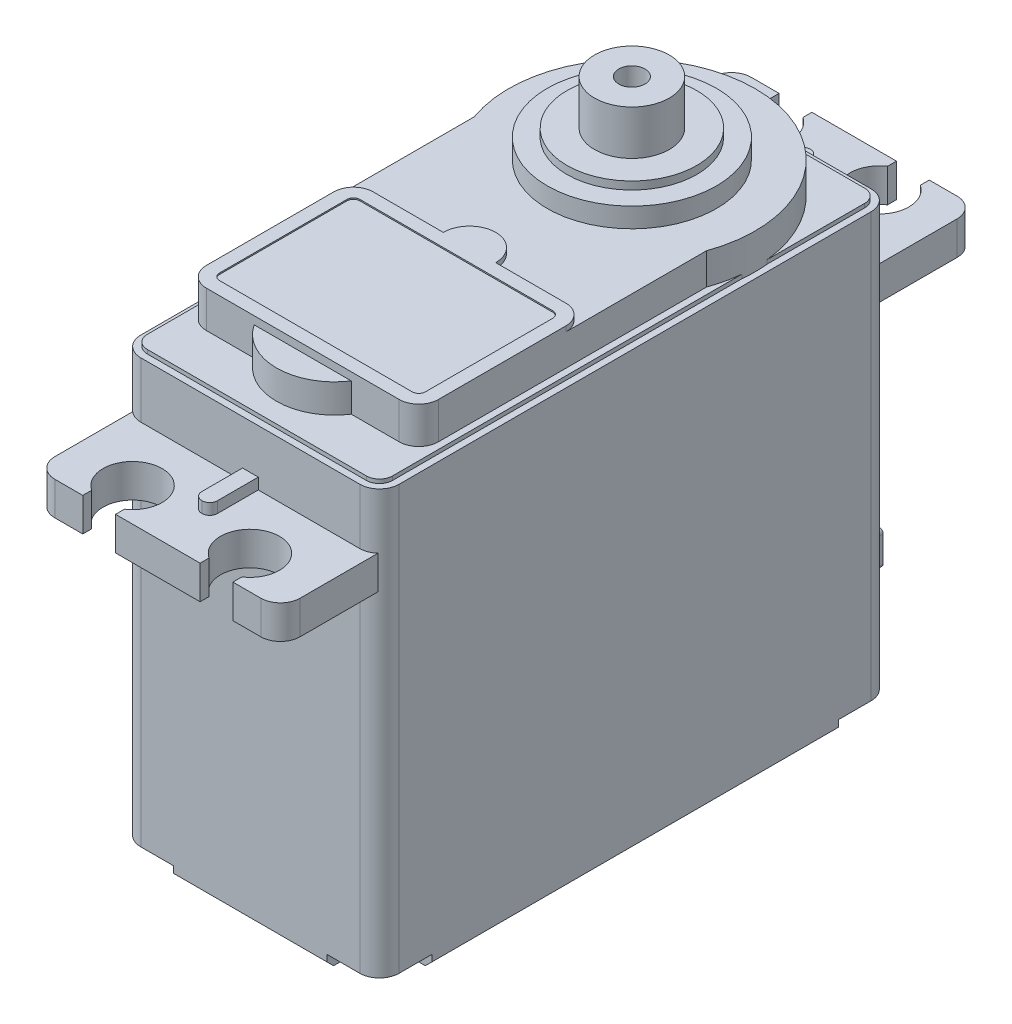
SolidWorks part; units mm, degrees
ref_plane "Front Plane" through (0, 0, 0) normal (0, 0, 1) x (1, 0, 0)
ref_plane "Top Plane" through (0, 0, 0) normal (0, 1, 0) x (1, 0, 0)
ref_plane "Right Plane" through (0, 0, 0) normal (1, 0, 0) x (0, 0, -1)
sketch "Sketch1" plane through (0, 0, 0) normal (0, 1, 0) x (1, 0, 0)
  line L1 (-8.35, -25.58) -> (8.35, -25.58)
  line L2 (-9.85, -24.08) -> (-9.85, 11.92)
  line L3 (-8.35, 13.42) -> (8.35, 13.42)
  line L4 (9.85, -24.08) -> (9.85, 11.92)
  line L5 (-9.85, -25.58) -> (9.85, 13.42) construction
  line L6 (-9.85, 13.42) -> (9.85, -25.58) construction
  arc A0 (-9.85, 11.92) -> (-8.35, 13.42) centre (-8.35, 11.92) cw
  arc A1 (8.35, 13.42) -> (9.85, 11.92) centre (8.35, 11.92) cw
  arc A2 (9.85, -24.08) -> (8.35, -25.58) centre (8.35, -24.08) cw
  arc A3 (-8.35, -25.58) -> (-9.85, -24.08) centre (-8.35, -24.08) cw
  point P0 (0, 0)
  dimension "D4" = 9.85
  dimension "D5" = 1.5
  dimension "D1" = 19.7
  dimension "D2" = 39
  dimension "D3" = 25.58
extrude "Boss-Extrude1" add sketch "Sketch1" along normal blind 33.3
ref_plane "Plane1" through (0, 26.5, 0) normal (0, 1, 0) x (1, 0, 0)
sketch "Sketch4" plane through (0, 26.5, 0) normal (0, 1, 0) x (1, 0, 0)
  line L0 (-5.725, 20.47) -> (-5.725, 19.7908)
  line L1 (-7.85, -32.63) -> (-5.725, -32.63)
  line L2 (-9.35, -31.13) -> (-9.35, 18.97)
  line L3 (-7.85, 20.47) -> (-5.725, 20.47)
  line L4 (9.35, -31.13) -> (9.35, 18.97)
  line L5 (-9.35, -32.63) -> (9.35, 20.47) construction
  line L6 (-9.35, 20.47) -> (9.35, -32.63) construction
  line L7 (-3.225, 20.47) -> (-3.225, 19.7908)
  line L8 (-3.225, 20.47) -> (3.225, 20.47)
  line L9 (-21.9271, -6.08) -> (21.9271, -6.08) construction
  line L10 (5.725, 20.47) -> (7.85, 20.47)
  line L11 (5.725, -32.63) -> (5.725, -31.9508)
  line L12 (3.225, -32.63) -> (3.225, -31.9508)
  line L13 (0, -25.58) -> (0, 13.42) construction
  line L14 (-8.35, -25.58) -> (8.35, -25.58) construction
  line L15 (8.35, 13.42) -> (-8.35, 13.42) construction
  line L16 (-3.225, -32.63) -> (3.225, -32.63)
  line L17 (3.225, 20.47) -> (3.225, 19.7908)
  line L18 (5.725, 20.47) -> (5.725, 19.7908)
  line L19 (-3.225, -32.63) -> (-3.225, -31.9508)
  line L20 (-5.725, -32.63) -> (-5.725, -31.9508)
  line L21 (5.725, -32.63) -> (7.85, -32.63)
  arc A0 (7.85, 20.47) -> (9.35, 18.97) centre (7.85, 18.97) cw
  arc A1 (9.35, -31.13) -> (7.85, -32.63) centre (7.85, -31.13) cw
  arc A2 (-7.85, -32.63) -> (-9.35, -31.13) centre (-7.85, -31.13) cw
  arc A3 (-9.35, 18.97) -> (-7.85, 20.47) centre (-7.85, 18.97) cw
  arc A4 (-5.725, 19.7908) -> (-3.225, 19.7908) centre (-4.475, 17.92) ccw
  arc A5 (5.725, -31.9508) -> (3.225, -31.9508) centre (4.475, -30.08) ccw
  arc A6 (5.725, 19.7908) -> (3.225, 19.7908) centre (4.475, 17.92) cw
  arc A7 (-5.725, -31.9508) -> (-3.225, -31.9508) centre (-4.475, -30.08) cw
  point P0 (0, -6.08)
  dimension "D3" = 1.5
  dimension "D4" = 2.5
  dimension "D5" = 2.25
  dimension "D1" = 18.7
  dimension "D2" = 53.1
  dimension "D6" = 0.6792
  dimension "D7" = 8.95
  dimension "D8" = 48
extrude "Boss-Extrude2" add sketch "Sketch4" along normal blind 2.55
sketch "Sketch5" plane through (0, 33.3, 0) normal (0, 1, 0) x (1, 0, 0)
  line L0 (8.35, -25.58) -> (-8.35, -25.58) construction
  line L2 (-8.85, 0.3518) -> (-8.85, -20.08)
  line L3 (-7.35, -21.58) -> (7.35, -21.58)
  line L4 (8.85, 0.3518) -> (8.85, -20.08)
  line L6 (0, 3.52) -> (0, 32.9422) construction
  arc A0 (8.85, 0.3518) -> (-8.85, 0.3518) centre (0, 3.52) ccw
  arc A1 (8.85, -20.08) -> (7.35, -21.58) centre (7.35, -20.08) cw
  arc A2 (-7.35, -21.58) -> (-8.85, -20.08) centre (-7.35, -20.08) cw
  dimension "D1" = 18.8
  dimension "D2" = 1.5
  dimension "D5" = 8.85
  dimension "D3" = 17.7
  dimension "D4" = 25.1
  dimension "D6" = 4
extrude "Boss-Extrude3" add sketch "Sketch5" along normal blind 2.7
sketch "Sketch6" plane through (0, 33.3, 0) normal (0, 1, 0) x (1, 0, 0)
  circle A0 centre (0, -19.1575) radius 4.4225
extrude "Boss-Extrude4" add sketch "Sketch6" along normal blind 2.5
sketch "Sketch7" plane through (0, 36, 0) normal (0, 1, 0) x (1, 0, 0)
  circle A0 centre (0, 3.52) radius 6.45
  dimension "D1" = 12.9
extrude "Boss-Extrude5" add sketch "Sketch7" along normal blind 1.5
sketch "Sketch8" plane through (0, 37.5, 0) normal (0, 1, 0) x (1, 0, 0)
  circle A2 centre (0, 3.52) radius 4.95
  circle A3 centre (0, 3.52) radius 4.95
  dimension "D1" = 1.5
extrude "Boss-Extrude6" add sketch "Sketch8" along normal blind 0.6
sketch "Sketch10" plane through (0, 38.1, 0) normal (0, 1, 0) x (1, 0, 0)
  circle A1 centre (0, 3.52) radius 2.85
  dimension "D1" = 5.7
extrude "Boss-Extrude7" add sketch "Sketch10" along normal blind 3.4
sketch "Sketch11" plane through (0, 29.05, 0) normal (0, 1, 0) x (1, 0, 0)
  line L0 (-8.35, 13.42) -> (8.35, 13.42) construction
  line L1 (0.61, 13.42) -> (-0.59, 13.42)
  line L2 (0.61, 13.42) -> (0.61, 16.53)
  line L3 (0.02, 17.12) -> (0, 17.12)
  line L4 (-0.59, 13.42) -> (-0.59, 16.53)
  line L5 (-9.35, 18.97) -> (-9.35, 13.038) construction
  line L6 (9.85, -6.08) -> (-9.85, -6.08) construction
  line L7 (9.85, -24.08) -> (9.85, 11.92) construction
  line L8 (-9.85, 11.92) -> (-9.85, -24.08) construction
  line L9 (-0.59, -25.58) -> (-0.59, -28.69)
  line L10 (0.02, -29.28) -> (0, -29.28)
  line L11 (0.61, -25.58) -> (0.61, -28.69)
  line L12 (0.61, -25.58) -> (-0.59, -25.58)
  arc A0 (0, 17.12) -> (-0.59, 16.53) centre (0, 16.53) ccw
  arc A1 (0.02, 17.12) -> (0.61, 16.53) centre (0.02, 16.53) cw
  arc A2 (0.02, -29.28) -> (0.61, -28.69) centre (0.02, -28.69) ccw
  arc A3 (0, -29.28) -> (-0.59, -28.69) centre (0, -28.69) cw
  point P8 (-0.59, 17.12)
  point P11 (0.61, 17.12)
  point P14 (-9.35, 16.004)
  point P29 (0.61, -29.28)
  point P30 (-0.59, -29.28)
  dimension "D3" = 0.59
  dimension "D1" = 1.2
  dimension "D2" = 3.7
  dimension "D4" = 9.35
extrude "Boss-Extrude8" add sketch "Sketch11" along normal blind 0.85
sketch "Sketch12" plane through (0, 41.5, 0) normal (0, 1, 0) x (1, 0, 0)
  circle A0 centre (0, 3.52) radius 1
  dimension "D1" = 2
extrude "Cut-Extrude1" cut sketch "Sketch12" against normal blind 5
sketch "Sketch13" plane through (0, 36, 0) normal (0, 1, 0) x (1, 0, 0)
  line L0 (-8.85, 0.3518) -> (-8.85, -20.08) construction
  line L1 (-7.35, -21.58) -> (7.35, -21.58) construction
  line L2 (8.85, -20.08) -> (8.85, 0.3518) construction
  line L3 (-8.85, -10.3641) -> (-8.85, -20.08)
  line L4 (-7.35, -21.58) -> (7.35, -21.58)
  line L5 (8.85, -20.08) -> (8.85, -10.3641)
  line L6 (-7.85, -10.3641) -> (-7.85, -20.08)
  line L7 (-7.35, -20.58) -> (7.35, -20.58)
  line L8 (7.85, -20.08) -> (7.85, -10.3641)
  line L9 (-7.35, -9.8641) -> (7.35, -9.8641)
  line L10 (-7.35, -8.8641) -> (-2, -8.8641)
  line L11 (2, -8.8641) -> (7.35, -8.8641)
  arc A0 (-8.85, -20.08) -> (-7.35, -21.58) centre (-7.35, -20.08) ccw construction
  arc A1 (7.35, -21.58) -> (8.85, -20.08) centre (7.35, -20.08) ccw construction
  arc A2 (-8.85, -20.08) -> (-7.35, -21.58) centre (-7.35, -20.08) ccw
  arc A3 (7.35, -21.58) -> (8.85, -20.08) centre (7.35, -20.08) ccw
  arc A4 (-7.85, -20.08) -> (-7.35, -20.58) centre (-7.35, -20.08) ccw
  arc A5 (7.35, -20.58) -> (7.85, -20.08) centre (7.35, -20.08) ccw
  arc A6 (7.35, -9.8641) -> (7.85, -10.3641) centre (7.35, -10.3641) cw
  arc A7 (-7.35, -9.8641) -> (-7.85, -10.3641) centre (-7.35, -10.3641) ccw
  arc A8 (7.35, -8.8641) -> (8.85, -10.3641) centre (7.35, -10.3641) cw
  arc A9 (-7.35, -8.8641) -> (-8.85, -10.3641) centre (-7.35, -10.3641) ccw
  arc A10 (2, -8.8641) -> (-2, -8.8641) centre (0, -8.8641) ccw
  point P8 (-7.85, 0.3518)
  point P15 (7.85, 0.3518)
  dimension "D2" = 0.5
  dimension "D1" = 1
  dimension "D3" = 1.5
  dimension "D4" = 4
extrude "Boss-Extrude9" add sketch "Sketch13" along normal blind 0.4
sketch "Sketch14" plane through (0, 36, 0) normal (0, 1, 0) x (1, 0, 0)
  line L4 (-7.85, -10.3641) -> (-7.85, -20.08)
  line L5 (-7.35, -20.58) -> (7.35, -20.58)
  line L6 (7.85, -20.08) -> (7.85, -10.3641)
  line L7 (7.35, -9.8641) -> (-7.35, -9.8641)
  line L8 (-7.85, -10.3641) -> (-7.85, -20.08)
  line L9 (-7.35, -20.58) -> (7.35, -20.58)
  line L10 (7.85, -20.08) -> (7.85, -10.3641)
  line L11 (7.35, -9.8641) -> (-7.35, -9.8641)
  arc A4 (-7.85, -20.08) -> (-7.35, -20.58) centre (-7.35, -20.08) ccw
  arc A5 (7.35, -20.58) -> (7.85, -20.08) centre (7.35, -20.08) ccw
  arc A6 (7.85, -10.3641) -> (7.35, -9.8641) centre (7.35, -10.3641) ccw
  arc A7 (-7.35, -9.8641) -> (-7.85, -10.3641) centre (-7.35, -10.3641) ccw
  arc A8 (-7.85, -20.08) -> (-7.35, -20.58) centre (-7.35, -20.08) ccw
  arc A9 (7.35, -20.58) -> (7.85, -20.08) centre (7.35, -20.08) ccw
  arc A10 (7.85, -10.3641) -> (7.35, -9.8641) centre (7.35, -10.3641) ccw
  arc A11 (-7.35, -9.8641) -> (-7.85, -10.3641) centre (-7.35, -10.3641) ccw
  dimension "D1" = 0
extrude "Boss-Extrude10" add sketch "Sketch14" along normal blind 0.3
sketch "Sketch16" plane through (0, 33.3, 0) normal (0, 1, 0) x (1, 0, 0)
  line L8 (-9.35, 11.92) -> (-9.35, -24.08)
  line L9 (-8.35, -25.08) -> (8.35, -25.08)
  line L10 (9.35, -24.08) -> (9.35, 11.92)
  line L11 (8.35, 12.92) -> (-8.35, 12.92)
  line L12 (-9.35, 11.92) -> (-9.35, -24.08)
  line L13 (-8.35, -25.08) -> (8.35, -25.08)
  line L14 (9.35, -24.08) -> (9.35, 11.92)
  line L15 (8.35, 12.92) -> (-8.35, 12.92)
  arc A8 (-8.35, 12.92) -> (-9.35, 11.92) centre (-8.35, 11.92) ccw
  arc A9 (-9.35, -24.08) -> (-8.35, -25.08) centre (-8.35, -24.08) ccw
  arc A10 (8.35, -25.08) -> (9.35, -24.08) centre (8.35, -24.08) ccw
  arc A11 (9.35, 11.92) -> (8.35, 12.92) centre (8.35, 11.92) ccw
  arc A12 (-8.35, 12.92) -> (-9.35, 11.92) centre (-8.35, 11.92) ccw
  arc A13 (-9.35, -24.08) -> (-8.35, -25.08) centre (-8.35, -24.08) ccw
  arc A14 (8.35, -25.08) -> (9.35, -24.08) centre (8.35, -24.08) ccw
  arc A15 (9.35, 11.92) -> (8.35, 12.92) centre (8.35, 11.92) ccw
  dimension "D1" = 0.5
extrude "Boss-Extrude11" add sketch "Sketch16" along normal blind 0.3
chamfer "Chamfer1" distance 0.5 angle 45 8 edges at (-9.85, 0, 6.08) (-9.4107, 0, 25.1407) (0, 0, 25.58) (9.4107, 0, 25.1407) (9.85, 0, 6.08) (9.4107, 0, -12.9807) (0, 0, -13.42) (-9.4107, 0, -12.9807)
sketch "Sketch17" plane through (0, 0, 0) normal (0, -1, 0) x (1, 0, 0)
  line L0 (-9.85, -11.92) -> (-9.85, 24.08) construction
  line L1 (-8.35, 25.58) -> (8.35, 25.58) construction
  line L3 (-9.85, 21.58) -> (-9.85, 24.08)
  line L4 (-8.35, 25.58) -> (-5.85, 25.58)
  line L5 (-5.85, 25.58) -> (-5.85, 23.08)
  line L6 (-7.35, 21.58) -> (-9.85, 21.58)
  arc A0 (-8.35, 25.58) -> (-9.85, 24.08) centre (-8.35, 24.08) ccw construction
  arc A3 (-8.35, 25.58) -> (-9.85, 24.08) centre (-8.35, 24.08) ccw
  arc A4 (-5.85, 23.08) -> (-7.35, 21.58) centre (-7.35, 23.08) cw
  point P10 (-5.85, 21.58)
  dimension "D3" = 1.5
  dimension "D1" = 4
  dimension "D2" = 4
extrude "Cut-Extrude2" cut sketch "Sketch17" against normal blind 1
mirror "Mirror1" about plane through (0, 0, 0) normal (1, 0, 0) of "Cut-Extrude2"
ref_plane "Plane2" through (0, 0, 6.08) normal (0, 0, 1) x (1, 0, 0)
mirror "Mirror2" about plane through (0, 0, 6.08) normal (0, 0, 1) of "Mirror1", "Cut-Extrude2"
sketch "Sketch19" plane through (0, 0, -13.42) normal (0, 0, -1) x (-1, 0, 0)
  line L1 (-2.5, 5.5) -> (2.5, 5.5)
  line L2 (-3.5, 4.5) -> (-3.5, 2.5)
  line L3 (-2.5, 1.5) -> (2.5, 1.5)
  line L4 (3.5, 4.5) -> (3.5, 2.5)
  line L6 (-5.85, 0.5) -> (5.85, 0.5) construction
  arc A0 (-3.5, 2.5) -> (-2.5, 1.5) centre (-2.5, 2.5) ccw
  arc A1 (2.5, 1.5) -> (3.5, 2.5) centre (2.5, 2.5) ccw
  arc A2 (2.5, 5.5) -> (3.5, 4.5) centre (2.5, 4.5) cw
  arc A3 (-2.5, 5.5) -> (-3.5, 4.5) centre (-2.5, 4.5) ccw
  point P8 (-3.5, 1.5)
  point P13 (3.5, 5.5)
  point P16 (-3.5, 5.5)
  dimension "D4" = 1
  dimension "D1" = 7
  dimension "D2" = 4
  dimension "D3" = 1
extrude "Boss-Extrude12" add sketch "Sketch19" along normal blind 1.5
sketch "Sketch20" plane through (0, 0, -14.92) normal (0, 0, -1) x (-1, 0, 0)
  line L8 (-2.5, 1.8) -> (2.5, 1.8)
  line L9 (3.2, 2.5) -> (3.2, 4.5)
  line L10 (2.5, 5.2) -> (-2.5, 5.2)
  line L11 (-3.2, 4.5) -> (-3.2, 2.5)
  line L12 (-2.5, 1.8) -> (2.5, 1.8)
  line L13 (3.2, 2.5) -> (3.2, 4.5)
  line L14 (2.5, 5.2) -> (-2.5, 5.2)
  line L15 (-3.2, 4.5) -> (-3.2, 2.5)
  arc A8 (-3.2, 2.5) -> (-2.5, 1.8) centre (-2.5, 2.5) ccw
  arc A9 (2.5, 1.8) -> (3.2, 2.5) centre (2.5, 2.5) ccw
  arc A10 (3.2, 4.5) -> (2.5, 5.2) centre (2.5, 4.5) ccw
  arc A11 (-2.5, 5.2) -> (-3.2, 4.5) centre (-2.5, 4.5) ccw
  arc A12 (-3.2, 2.5) -> (-2.5, 1.8) centre (-2.5, 2.5) ccw
  arc A13 (2.5, 1.8) -> (3.2, 2.5) centre (2.5, 2.5) ccw
  arc A14 (3.2, 4.5) -> (2.5, 5.2) centre (2.5, 4.5) ccw
  arc A15 (-2.5, 5.2) -> (-3.2, 4.5) centre (-2.5, 4.5) ccw
  dimension "D1" = 0.3
extrude "Boss-Extrude13" add sketch "Sketch20" along normal blind 5 draft 5
